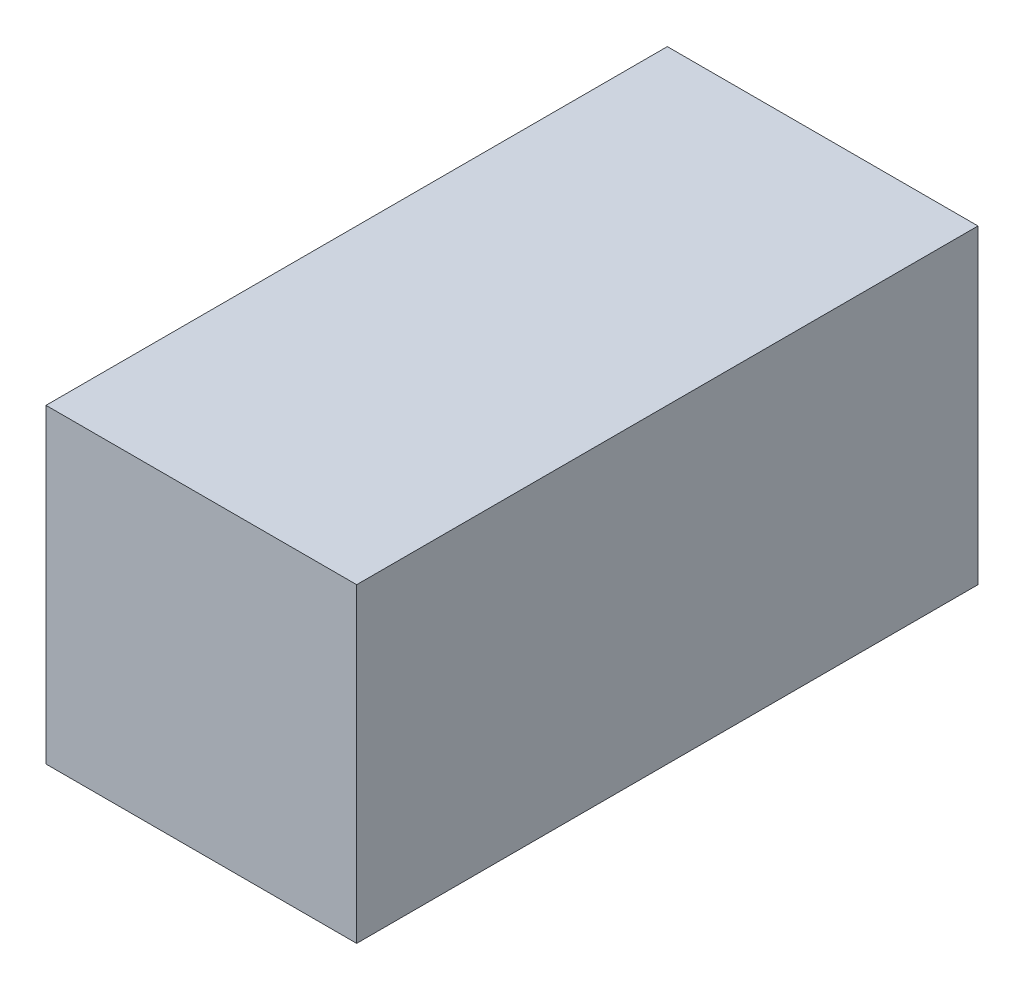
SolidWorks part; units mm, degrees
ref_plane "Face" through (0, 0, 0) normal (0, 0, 1) x (1, 0, 0)
ref_plane "Dessus" through (0, 0, 0) normal (0, 1, 0) x (1, 0, 0)
ref_plane "Droite" through (0, 0, 0) normal (1, 0, 0) x (0, 0, -1)
sketch "Esquisse1" plane through (0, 0, 0) normal (0, 0, 1) x (1, 0, 0)
  line L1 (0, 0) -> (22, 0)
  line L2 (0, 0) -> (0, 22)
  line L3 (0, 22) -> (22, 22)
  line L4 (22, 0) -> (22, 22)
  dimension "D1" = 22
  dimension "D2" = 22
extrude "Extrusion1" add sketch "Esquisse1" against normal blind 44
